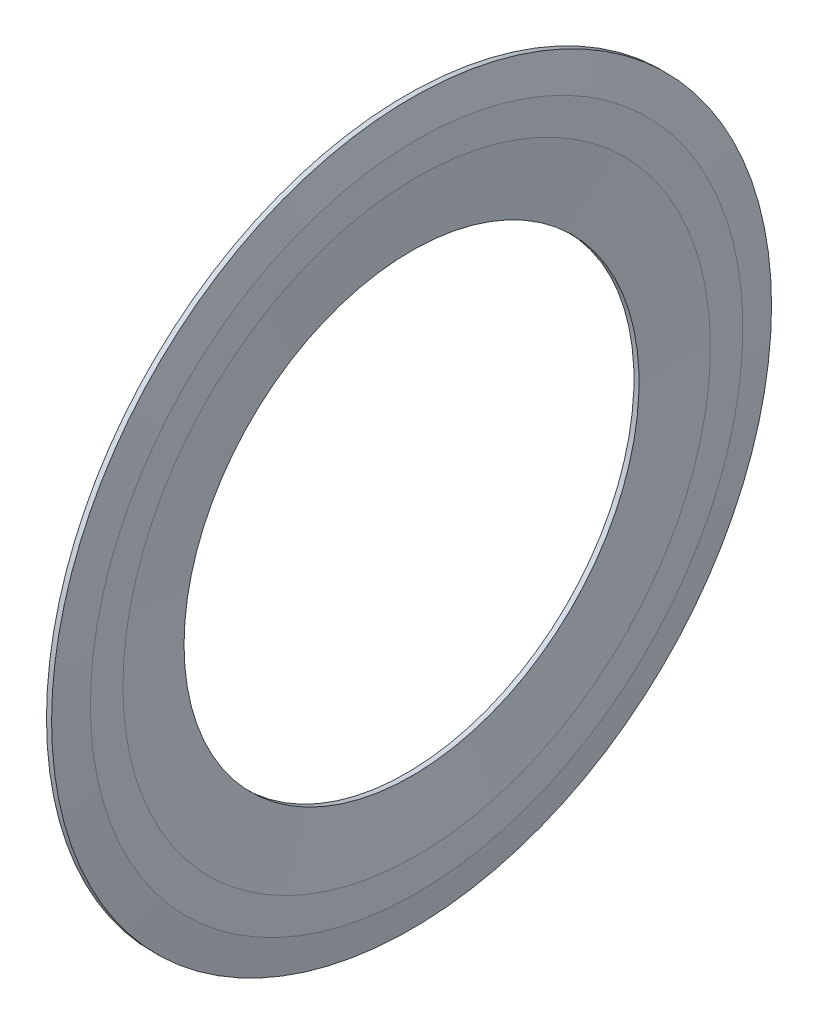
SolidWorks part; units mm, degrees
ref_plane "Front Plane" through (0, 0, 0) normal (0, 0, 1) x (1, 0, 0)
ref_plane "Top Plane" through (0, 0, 0) normal (0, 1, 0) x (1, 0, 0)
ref_plane "Right Plane" through (0, 0, 0) normal (1, 0, 0) x (0, 0, -1)
ref_plane "Plane1" through (0, 0, 0) normal (0, 0, 1) x (1, 0, 0)
sketch "Sketch1" plane through (0, 0, 0) normal (0, 0, 1) x (1, 0, 0)
  line L0 (0.53, 7.9) -> (0.707, 7.9)
  line L1 (0.707, 7.9) -> (0.884, 10.2)
  line L2 (0.884, 10.2) -> (0.884, 11.3296)
  line L3 (0.884, 11.3296) -> (0.707, 12.5)
  line L4 (0.707, 12.5) -> (0.53, 12.5)
  line L5 (0.53, 12.5) -> (0.6185, 11.35)
  line L6 (0.6185, 11.35) -> (0.53, 10.2)
  line L7 (0.53, 10.2) -> (0.53, 7.9)
  line L8 (0.707, 0) -> (0.53, 0) construction
revolve "Revolve1" add sketch "Sketch1" angle 360 about L8
